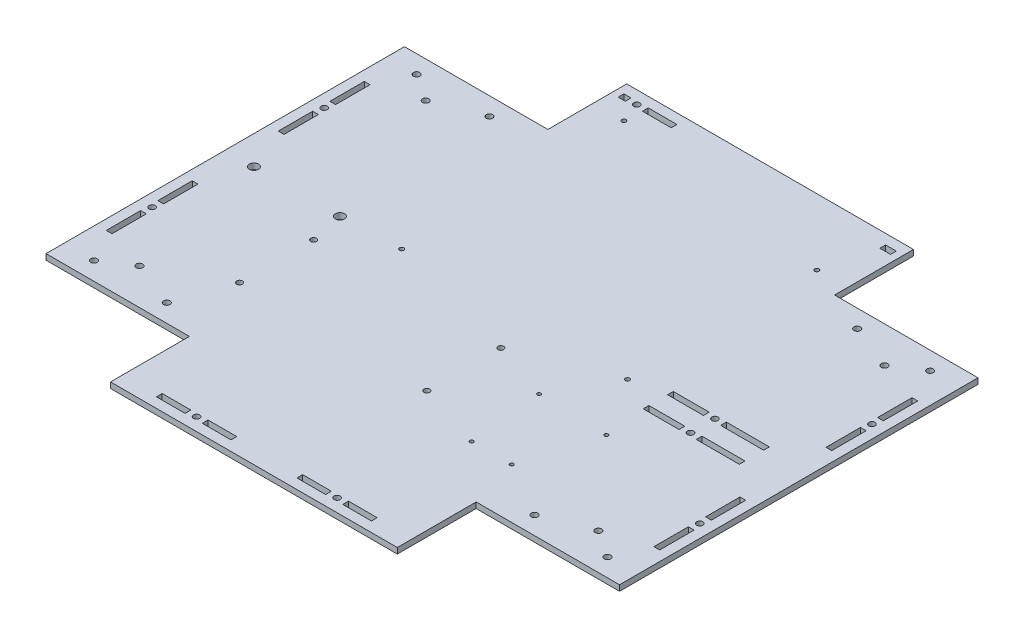
SolidWorks part; units mm, degrees
ref_plane "Front Plane" through (0, 0, 0) normal (0, 0, 1) x (1, 0, 0)
ref_plane "Top Plane" through (0, 0, 0) normal (0, 1, 0) x (1, 0, 0)
ref_plane "Right Plane" through (0, 0, 0) normal (1, 0, 0) x (0, 0, -1)
sketch "Sketch1" plane through (0, 0, 0) normal (0, 1, 0) x (1, 0, 0)
  line L1 (-200, 180) -> (200, 180)
  line L2 (-200, 180) -> (-200, -180)
  line L3 (-200, -180) -> (200, -180)
  line L4 (200, 180) -> (200, -180)
  line L5 (-200, 180) -> (200, -180) construction
  line L6 (-200, -180) -> (200, 180) construction
  point P0 (0, 0)
  dimension "D1" = 400
  dimension "D2" = 360
extrude "Boss-Extrude1" add sketch "Sketch1" along normal blind 4
sketch "Sketch2" plane through (0, 4, 0) normal (0, 1, 0) x (1, 0, 0)
  line L1 (-200, 180) -> (-100, 180)
  line L2 (-200, 180) -> (-200, 125)
  line L3 (-200, 125) -> (-100, 125)
  line L4 (-100, 180) -> (-100, 125)
  dimension "D1" = 100
  dimension "D2" = 55
extrude "Corner" cut sketch "Sketch2" against normal up to next (4 mm away)
sketch "Sketch3" plane through (0, 4, 0) normal (0, 1, 0) x (1, 0, 0)
  line L0 (-100, 125) -> (-220, 125) construction
  line L1 (-160, 125) -> (-160, 39.7027) construction
  circle A0 centre (-179.05, 112.5) radius 2.25
  circle A1 centre (-128.25, 112.5) radius 2.25
  circle A2 centre (-160, 99.8) radius 2.25
  dimension "D2" = 4.5
  dimension "D3" = 4.5
  dimension "D6" = 4.5
  dimension "D1" = 120
  dimension "D4" = 50.8
  dimension "D5" = 19.05
  dimension "D7" = 12.5
  dimension "D8" = 12.7
extrude "Motor mounting" cut sketch "Sketch3" against normal up to next (4 mm away)
mirror "Mirror1" about plane through (0, 0, 0) normal (0, 0, 1) of "Motor mounting", "Corner"
sketch "Sketch4" plane through (0, 4, 0) normal (0, 1, 0) x (1, 0, 0)
  line L1 (0, 0) -> (-200, 0) construction
  line L2 (-146.35, -35) -> (-133.65, -35) construction
  line L3 (-146.35, -32.5) -> (-133.65, -32.5)
  line L4 (-146.35, -37.5) -> (-133.65, -37.5)
  line L6 (-140, -23.5) -> (-140, -46.5) construction
  line L7 (-146.35, -25.5) -> (-133.65, -25.5)
  line L8 (-146.35, -25.5) -> (-146.35, -23.5)
  line L9 (-146.35, -23.5) -> (-133.65, -23.5)
  line L10 (-133.65, -25.5) -> (-133.65, -23.5)
  line L11 (-146.35, -44.5) -> (-133.65, -44.5)
  line L12 (-146.35, -44.5) -> (-146.35, -46.5)
  line L13 (-146.35, -46.5) -> (-133.65, -46.5)
  line L14 (-133.65, -44.5) -> (-133.65, -46.5)
  line L15 (-200, 125) -> (-200, -125) construction
  line L16 (-200, 125) -> (-200, -125) construction
  line L17 (-146.35, -23.5) -> (-146.35, -46.5) construction
  arc A1 (-146.35, -32.5) -> (-146.35, -37.5) centre (-146.35, -35) ccw
  arc A2 (-133.65, -37.5) -> (-133.65, -32.5) centre (-133.65, -35) ccw
  point P4 (-140, -35)
  dimension "D1" = 5
  dimension "D2" = 12.7
  dimension "D3" = 35
  dimension "D4" = 9.5
  dimension "D5" = 9.5
  dimension "D6" = 2
  dimension "D7" = 2
  dimension "D8" = 60
  dimension "D9" = 90
mirror "Mirror2" about plane through (0, 0, 0) normal (1, 0, 0) of "Corner", "Motor mounting", "Mirror1"
sketch "Sketch5" plane through (0, 4, 0) normal (0, 1, 0) x (1, 0, 0)
  line L0 (-78.74, 133.87) -> (-78.74, 156.73) construction
  line L1 (-78.74, 133.87) -> (78.74, 133.87) construction
  line L2 (-78.74, 133.87) -> (-78.74, 1.79) construction
  line L3 (-78.74, 1.79) -> (78.74, 1.79) construction
  line L4 (78.74, 133.87) -> (78.74, 1.79) construction
  line L5 (-78.74, 133.87) -> (78.74, 1.79) construction
  line L6 (-78.74, 1.79) -> (78.74, 133.87) construction
  line L8 (100, 180) -> (-100, 180) construction
  circle A0 centre (-78.74, 156.73) radius 1.5
  circle A1 centre (78.74, 133.87) radius 1.5
  circle A2 centre (-78.74, 1.79) radius 1.5
  circle A3 centre (78.74, 1.79) radius 1.5
  point P0 (0, 67.83)
  dimension "D5" = 3
  dimension "D6" = 3
  dimension "D7" = 3
  dimension "D8" = 3
  dimension "D1" = 132.08
  dimension "D2" = 157.48
  dimension "D3" = 22.86
  dimension "D4" = 23.27
extrude "PC mounting" cut sketch "Sketch5" against normal up to next
sketch "Sketch6" plane through (0, 4, 0) normal (0, 1, 0) x (1, 0, 0)
  line L2 (100, -125) -> (100, -180) construction
  line L3 (200, -125) -> (100, -125) construction
  line L7 (56.8, -39.2) -> (56.8, -37.9) construction
  line L8 (56.8, -39.2) -> (56.8, -90) construction
  line L9 (56.8, -39.2) -> (105, -39.2) construction
  line L10 (105, -39.2) -> (105, -90) construction
  line L11 (56.8, -90) -> (105, -90) construction
  line L12 (56.8, -37.9) -> (105, -37.9) construction
  line L13 (105, -37.9) -> (105, -39.2) construction
  line L14 (61.9, -90) -> (61.9, -39.2) construction
  line L15 (89.8, -90) -> (89.8, -39.2) construction
  circle A0 centre (56.8, -37.9) radius 1.25
  circle A1 centre (105, -39.2) radius 1.25
  circle A6 centre (89.8, -90) radius 1.25
  circle A7 centre (61.9, -90) radius 1.25
  dimension "D3" = 5
  dimension "D8" = 1.3
  dimension "D9" = 48.2
  dimension "D10" = 5.1
  dimension "D2" = 35
  dimension "D7" = 50.8
  dimension "D11" = 15.2
extrude "Arduino mounting" cut sketch "Sketch6" against normal up to next
sketch "Sketch7" plane through (0, 4, 0) normal (0, 1, 0) x (1, 0, 0)
  line L0 (-115, -75) -> (15.6, -75) construction
  line L1 (-115, -75) -> (-115, -23.4) construction
  line L2 (-100, -180) -> (100, -180) construction
  line L3 (-100, -125) -> (-100, -180) construction
  circle A0 centre (-115, -75) radius 2
  circle A1 centre (15.6, -75) radius 2
  circle A2 centre (-115, -23.4) radius 2
  circle A3 centre (15.6, -23.4) radius 2
  dimension "D1" = 4
  dimension "D2" = 2
  dimension "D3" = 2
  dimension "D4" = 2
  dimension "D5" = 51.6
  dimension "D6" = 105
  dimension "D7" = 15
extrude "DCDC-USB mounting" cut sketch "Sketch7" against normal up to next
sketch "Sketch10" plane through (0, 4, 0) normal (0, 1, 0) x (1, 0, 0)
  line L0 (-95, 169) -> (95, 169) construction
  line L2 (-78, 173) -> (-58, 173)
  line L3 (189, 125) -> (189, -125) construction
  line L4 (200, 125) -> (100, 125) construction
  line L5 (200, -125) -> (100, -125) construction
  line L6 (-100, -169) -> (100, -169) construction
  line L7 (-100, -125) -> (-100, -180) construction
  line L8 (100, -125) -> (100, -180) construction
  line L9 (-189, 125) -> (-189, -125) construction
  line L10 (-200, 125) -> (-100, 125) construction
  line L11 (-200, -125) -> (-100, -125) construction
  line L12 (100, 180) -> (-100, 180) construction
  line L13 (-78, 173) -> (-78, 169)
  line L14 (-78, 169) -> (-58, 169)
  line L15 (-58, 173) -> (-58, 169)
  line L16 (-200, 125) -> (-200, -125) construction
  line L17 (-100, -180) -> (100, -180) construction
  line L18 (200, -125) -> (200, 125) construction
  line L19 (-95, 173) -> (95, 173) construction
  line L20 (-193, -125) -> (-193, 125) construction
  line L21 (193, 125) -> (193, -125) construction
  line L22 (-100, -173) -> (100, -173) construction
  line L23 (-193, 90) -> (193, 90) construction
  line L24 (-193, -90) -> (193, -90) construction
  line L25 (-193, 30) -> (193, 30) construction
  line L26 (-193, -30) -> (193, -30) construction
  line L27 (-193, 66) -> (193, 66) construction
  line L28 (-193, 54) -> (193, 54) construction
  line L29 (-193, -54) -> (193, -54) construction
  line L30 (-193, -66) -> (193, -66) construction
  line L31 (-71.22, 180) -> (-71.22, 152.9393) construction
  line L32 (-193, 90) -> (-189, 90)
  line L33 (-193, 90) -> (-193, 66)
  line L34 (-193, 66) -> (-189, 66)
  line L35 (-189, 90) -> (-189, 66)
  line L36 (-193, -30) -> (-189, -30)
  line L37 (-193, -30) -> (-193, -54)
  line L38 (-193, -54) -> (-189, -54)
  line L39 (-189, -30) -> (-189, -54)
  line L40 (-193, -66) -> (-189, -66)
  line L41 (-193, -66) -> (-193, -90)
  line L42 (-193, -90) -> (-189, -90)
  line L43 (-189, -66) -> (-189, -90)
  line L44 (-193, 54) -> (-189, 54)
  line L45 (-193, 54) -> (-193, 30)
  line L46 (-193, 30) -> (-189, 30)
  line L47 (-189, 54) -> (-189, 30)
  line L48 (193, 90) -> (189, 90)
  line L49 (193, 90) -> (193, 66)
  line L50 (193, 66) -> (189, 66)
  line L51 (189, 90) -> (189, 66)
  line L52 (193, 54) -> (189, 54)
  line L53 (193, 54) -> (193, 30)
  line L54 (193, 30) -> (189, 30)
  line L55 (189, 54) -> (189, 30)
  line L56 (193, -30) -> (189, -30)
  line L57 (193, -30) -> (193, -54)
  line L58 (193, -54) -> (189, -54)
  line L59 (189, -30) -> (189, -54)
  line L60 (193, -66) -> (189, -66)
  line L61 (193, -66) -> (193, -90)
  line L62 (193, -90) -> (189, -90)
  line L63 (189, -66) -> (189, -90)
  line L64 (-75, -169) -> (-55, -169)
  line L65 (-75, -169) -> (-75, -173)
  line L66 (-75, -173) -> (-55, -173)
  line L67 (-55, -169) -> (-55, -173)
  line L68 (-43, -169) -> (-23, -169)
  line L69 (-43, -169) -> (-43, -173)
  line L70 (-43, -173) -> (-23, -173)
  line L71 (-23, -169) -> (-23, -173)
  line L72 (23, -169) -> (43, -169)
  line L73 (23, -169) -> (23, -173)
  line L74 (23, -173) -> (43, -173)
  line L75 (43, -169) -> (43, -173)
  line L76 (55, -169) -> (75, -169)
  line L77 (55, -169) -> (55, -173)
  line L78 (55, -173) -> (75, -173)
  line L79 (75, -169) -> (75, -173)
  line L80 (87.53, 180) -> (87.53, 152.9393) construction
  line L81 (-100, 125) -> (-100, 180) construction
  line L82 (-95, 173) -> (-90, 173)
  line L83 (-95, 173) -> (-95, 169)
  line L84 (-95, 169) -> (-90, 169)
  line L85 (-90, 173) -> (-90, 169)
  line L86 (95, 173) -> (87.53, 173)
  line L87 (95, 173) -> (95, 169)
  line L88 (95, 169) -> (87.53, 169)
  line L89 (87.53, 173) -> (87.53, 169)
  line L90 (100, 125) -> (100, 180) construction
  circle A2 centre (-78.74, 156.73) radius 1.5 construction
  dimension "D25" = 7.52
  dimension "D1" = 11
  dimension "D2" = 11
  dimension "D3" = 11
  dimension "D4" = 11
  dimension "D5" = 4
  dimension "D6" = 4
  dimension "D7" = 4
  dimension "D8" = 4
  dimension "D9" = 35
  dimension "D10" = 60
  dimension "D11" = 60
  dimension "D12" = 35
  dimension "D13" = 12
  dimension "D14" = 24
  dimension "D15" = 12
  dimension "D16" = 24
  dimension "D17" = 20
  dimension "D18" = 20
  dimension "D19" = 12
  dimension "D20" = 20
  dimension "D21" = 20
  dimension "D22" = 12
  dimension "D23" = 25
  dimension "D24" = 25
  dimension "D26" = 158.75
  dimension "D27" = 5
  dimension "D28" = 5
  dimension "D29" = 5
  dimension "D30" = 12
  dimension "D31" = 20
extrude "Sides mounting" cut sketch "Sketch10" against normal through all
sketch "Sketch11" plane through (0, 4, 0) normal (0, 1, 0) x (1, 0, 0)
  line L0 (200, 8.5) -> (0, 8.5) construction
  line L2 (189, -30) -> (189, -54) construction
  line L3 (139, 10.5) -> (169, 10.5)
  line L4 (139, 10.5) -> (139, 6.5)
  line L5 (139, 6.5) -> (169, 6.5)
  line L6 (169, 10.5) -> (169, 6.5)
  line L7 (139, 10.5) -> (169, 6.5) construction
  line L8 (139, 6.5) -> (169, 10.5) construction
  line L9 (102, 10.5) -> (127, 10.5)
  line L10 (102, 10.5) -> (102, 6.5)
  line L11 (102, 6.5) -> (127, 6.5)
  line L12 (127, 10.5) -> (127, 6.5)
  line L13 (102, 10.5) -> (127, 6.5) construction
  line L14 (102, 6.5) -> (127, 10.5) construction
  line L15 (0, 0) -> (200, 0) construction
  line L16 (200, -125) -> (200, 125) construction
  line L17 (102, -6.5) -> (127, -10.5) construction
  line L18 (102, -10.5) -> (127, -6.5) construction
  line L19 (139, -6.5) -> (169, -10.5) construction
  line L20 (139, -10.5) -> (169, -6.5) construction
  line L21 (127, -10.5) -> (127, -6.5)
  line L22 (102, -6.5) -> (127, -6.5)
  line L23 (102, -10.5) -> (102, -6.5)
  line L24 (102, -10.5) -> (127, -10.5)
  line L25 (169, -10.5) -> (169, -6.5)
  line L26 (139, -6.5) -> (169, -6.5)
  line L27 (139, -10.5) -> (139, -6.5)
  line L28 (139, -10.5) -> (169, -10.5)
  point P5 (154, 8.5)
  point P10 (114.5, 8.5)
  point P28 (114.5, -8.5)
  point P29 (154, -8.5)
  dimension "D1" = 4
  dimension "D2" = 12
  dimension "D3" = 30
  dimension "D4" = 25
  dimension "D5" = 20
  dimension "D6" = 8.5
extrude "fin mounting" cut sketch "Sketch11" against normal through all
hole_wizard "M4 Clearance Hole1" positions "Sketch13" profile "Sketch12" hole size "M4" standard "DIN"
sketch "Sketch13" plane through (0, 4, 0) normal (0, 1, 0) x (-1, 0, 0)
  line L4 (55, 171) -> (43, 171) construction
  line L5 (55, 173) -> (55, 169) construction
  line L6 (43, 169) -> (43, 173) construction
  line L8 (-43, 171) -> (-55, 171) construction
  line L9 (-43, 173) -> (-43, 169) construction
  line L10 (-55, 169) -> (-55, 173) construction
  line L12 (191, 90) -> (191, 30) construction
  line L13 (193, 90) -> (189, 90) construction
  line L14 (189, 30) -> (193, 30) construction
  line L16 (-191, -30) -> (-191, -90) construction
  line L17 (-189, -30) -> (-193, -30) construction
  line L18 (-193, -90) -> (-189, -90) construction
  line L24 (-127, -8.5) -> (-139, -8.5) construction
  line L25 (-127, -6.5) -> (-127, -10.5) construction
  line L26 (-139, -10.5) -> (-139, -6.5) construction
  line L27 (90, -171) -> (78, -171) construction
  line L28 (90, -169) -> (90, -173) construction
  line L29 (78, -173) -> (78, -169) construction
  line L30 (-127, 8.5) -> (-139, 8.5) construction
  line L31 (-127, 10.5) -> (-127, 6.5) construction
  line L32 (-139, 6.5) -> (-139, 10.5) construction
  point P0 (49, 171)
  point P29 (-49, 171)
  point P32 (191, 60)
  point P34 (191, -60)
  point P36 (-133, -8.5)
  point P38 (-191, -60)
  point P40 (-191, 60)
  point P80 (84, -171)
  point P96 (-133, 8.5)
sketch "Sketch12" plane through (-49, 4, 171) normal (1, 0, 0) x (0, 0, 1)
  line L0 (0, 0) -> (0, 7.2919)
  line L1 (0, 7.2919) -> (2.15, 6)
  line L2 (2.15, 6) -> (2.15, 0)
  line L5 (2.15, 0) -> (0, 0)
  line L10 (0, 7.2919) -> (-2.15, 6) construction
  line L11 (0, -6.35) -> (0, 107.95) construction
  dimension "Hole Dia." = 4.3
  dimension "Hole Depth" = 6
  dimension "Drill Angle" = 118
hole_wizard "M6 Clearance Hole1" positions "Sketch15" profile "Sketch14" hole size "M6" standard "DIN"
sketch "Sketch15" plane through (0, 4, 0) normal (0, 1, 0) x (-1, 0, 0)
  line L0 (200, 0) -> (53.4774, 0) construction
  line L1 (200, -125) -> (200, 125) construction
  point P0 (180, 0)
  point P1 (120, 0)
  dimension "D1" = 20
  dimension "D2" = 60
sketch "Sketch14" plane through (-180, 4, 0) normal (1, 0, 0) x (0, 0, 1)
  line L0 (0, 0) -> (0, 7.9228)
  line L1 (0, 7.9228) -> (3.2, 6)
  line L2 (3.2, 6) -> (3.2, 0)
  line L5 (3.2, 0) -> (0, 0)
  line L10 (0, 7.9228) -> (-3.2, 6) construction
  line L11 (0, -6.35) -> (0, 107.95) construction
  dimension "Hole Dia." = 6.4
  dimension "Hole Depth" = 6
  dimension "Drill Angle" = 118
equation "\"D2@Sketch10\" = \"D1@Sketch10\""
equation "\"D4@Sketch10\" = \"D1@Sketch10\""
equation "\"D3@Sketch10\" = \"D1@Sketch10\""
equation "\"D8@Sketch10\" = \"D5@Sketch10\""
equation "\"D6@Sketch10\"=\"D5@Sketch10\""
equation "\"D7@Sketch10\"=\"D5@Sketch10\""
